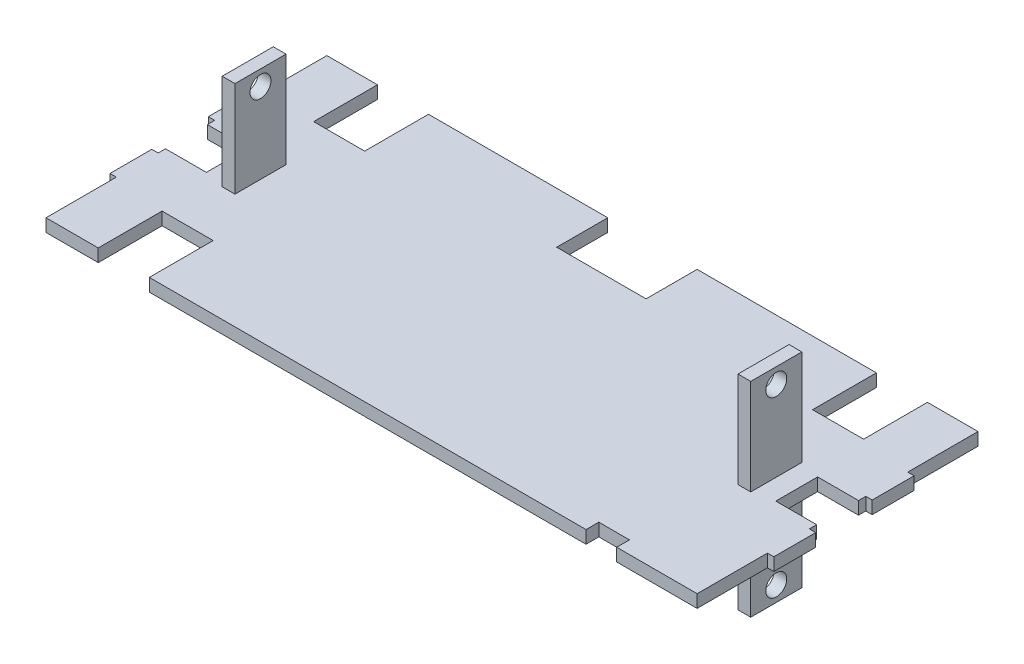
SolidWorks part; units mm, degrees
ref_plane "Front Plane" through (0, 0, 0) normal (0, 0, 1) x (1, 0, 0)
ref_plane "Top Plane" through (0, 0, 0) normal (0, 1, 0) x (1, 0, 0)
ref_plane "Right Plane" through (0, 0, 0) normal (1, 0, 0) x (0, 0, -1)
sketch "Sketch1" plane through (0, 0, 0) normal (0, 1, 0) x (1, 0, 0)
  line L1 (161.925, -69.85) -> (121.92, -69.85)
  line L2 (161.925, -69.85) -> (161.925, -34.8747)
  line L3 (161.925, 69.85) -> (136.779, 69.85)
  line L4 (-161.925, -69.85) -> (-161.925, -34.8747)
  line L5 (161.925, -69.85) -> (-161.925, 69.85) construction
  line L6 (161.925, 69.85) -> (-161.925, -69.85) construction
  line L7 (161.925, 10.414) -> (141.605, 10.414)
  line L9 (161.925, -10.414) -> (141.605, -10.414)
  line L10 (141.605, 10.414) -> (141.605, -10.414)
  line L11 (-136.779, 69.85) -> (-161.925, 69.85)
  line L13 (-161.925, -10.414) -> (-141.605, -10.414)
  line L14 (-141.605, 10.414) -> (-141.605, -10.414)
  line L15 (-161.925, 10.414) -> (-141.605, 10.414)
  line L17 (-141.605, 0) -> (141.605, 0) construction
  line L18 (-161.925, 14.0467) -> (-165.1, 14.0467)
  line L20 (-161.925, 34.8747) -> (-165.1, 34.8747)
  line L21 (-165.1, 14.0467) -> (-165.1, 34.8747)
  line L22 (-161.925, -34.8747) -> (-165.1, -34.8747)
  line L23 (-165.1, -14.0467) -> (-165.1, -34.8747)
  line L24 (-161.925, -14.0467) -> (-165.1, -14.0467)
  line L27 (161.925, -14.0467) -> (165.1, -14.0467)
  line L28 (165.1, -14.0467) -> (165.1, -34.8747)
  line L29 (161.925, -34.8747) -> (165.1, -34.8747)
  line L30 (161.925, 34.8747) -> (165.1, 34.8747)
  line L31 (165.1, 14.0467) -> (165.1, 34.8747)
  line L32 (161.925, 14.0467) -> (165.1, 14.0467)
  line L34 (-161.925, 34.8747) -> (-161.925, 69.85)
  line L35 (-161.925, -14.0467) -> (-161.925, -10.414)
  line L36 (161.925, 34.8747) -> (161.925, 69.85)
  line L37 (161.925, -14.0467) -> (161.925, -10.414)
  line L38 (-161.925, 10.414) -> (-161.925, 14.0467)
  line L39 (161.925, 10.414) -> (161.925, 14.0467)
  line L40 (-136.779, 69.85) -> (-136.779, 38.1)
  line L41 (-136.779, 38.1) -> (-111.379, 38.1)
  line L42 (-111.379, 69.85) -> (-111.379, 38.1)
  line L44 (111.379, 69.85) -> (111.379, 38.1)
  line L45 (111.379, 38.1) -> (136.779, 38.1)
  line L46 (136.779, 69.85) -> (136.779, 38.1)
  line L47 (111.379, 69.85) -> (22.2286, 69.85)
  line L48 (106.68, -69.85) -> (-106.68, -69.85)
  line L50 (106.68, -69.85) -> (106.68, -63.5)
  line L51 (106.68, -63.5) -> (121.92, -63.5)
  line L52 (121.92, -69.85) -> (121.92, -63.5)
  line L56 (-135.9408, -69.85) -> (-161.925, -69.85)
  line L57 (-106.68, -69.85) -> (-110.5408, -69.85)
  line L59 (-135.9408, -69.85) -> (-135.9408, -38.1)
  line L60 (-135.9408, -38.1) -> (-110.5408, -38.1)
  line L61 (-110.5408, -69.85) -> (-110.5408, -38.1)
  line L62 (-22.2286, 69.85) -> (-111.379, 69.85)
  line L64 (22.2286, 69.85) -> (22.2286, 44.45)
  line L65 (22.2286, 44.45) -> (-22.2286, 44.45)
  line L66 (-22.2286, 69.85) -> (-22.2286, 44.45)
  line L69 (0, 44.45) -> (0, -70.0261) construction
  point P0 (0, 0)
  point P6 (141.605, 0)
  point P11 (141.605, 0)
  point P47 (121.92, -66.675)
  point P48 (124.079, 38.1)
  point P49 (-124.079, 38.1)
  point P50 (0, 63.5)
  point P52 (-123.2408, -38.1)
  point P62 (0, 44.45)
  point P63 (0, 0)
  dimension "D1" = 323.85
  dimension "D2" = 139.7
  dimension "D3" = 20.828
  dimension "D5" = 3.175
  dimension "D6" = 20.828
  dimension "D4" = 20.32
  dimension "D7" = 31.75
  dimension "D8" = 25.4
  dimension "D9" = 25.4
  dimension "D10" = 31.75
  dimension "D13" = 15.24
  dimension "D14" = 6.35
  dimension "D15" = 40.005
  dimension "D16" = 25.4
  dimension "D17" = 31.75
  dimension "D18" = 41.8592
  dimension "D11" = 41.021
  dimension "D12" = 41.021
  dimension "D19" = 25.4
  dimension "D20" = 44.4572
  dimension "D21" = 3.6327
  dimension "D22" = 3.6327
  dimension "D25" = 20.828
  dimension "D26" = 20.828
  dimension "D28" = 20.828
  dimension "D29" = 3.6327
  dimension "D30" = 20.828
  dimension "D31" = 3.6327
  dimension "D32" = 20.828
  dimension "D23" = 20.32
extrude "Boss-Extrude1" add sketch "Sketch1" along normal mid plane 6.35
sketch "Sketch2" plane through (0, 0, 0) normal (0, 1, 0) x (1, 0, 0)
  line L0 (-141.605, 10.414) -> (-141.605, -10.414) construction
  line L1 (125.095, -12.7) -> (131.445, -12.7)
  line L2 (125.095, -12.7) -> (125.095, 12.7)
  line L3 (125.095, 12.7) -> (131.445, 12.7)
  line L4 (131.445, -12.7) -> (131.445, 12.7)
  line L5 (125.095, -12.7) -> (131.445, 12.7) construction
  line L6 (125.095, 12.7) -> (131.445, -12.7) construction
  line L9 (-125.095, -12.7) -> (-125.095, 12.7)
  line L10 (-125.095, 12.7) -> (-131.445, 12.7)
  line L11 (-131.445, -12.7) -> (-131.445, 12.7)
  line L12 (-125.095, -12.7) -> (-131.445, -12.7)
  line L13 (141.605, -10.414) -> (141.605, 10.414) construction
  point P0 (128.27, 0)
  point P10 (141.605, 0)
  dimension "D1" = 10.16
  dimension "D2" = 10.16
  dimension "D3" = 25.4
  dimension "D4" = 25.4
  dimension "D5" = 6.35
  dimension "D6" = 6.35
  dimension "D7" = 6.35
extrude "Boss-Extrude2" add sketch "Sketch2" along normal mid plane 101.6
sketch "Sketch3" plane through (-131.445, 0, 0) normal (-1, 0, 0) x (0, 0, 1)
  line L0 (-12.7, 50.8) -> (12.7, 50.8) construction
  line L1 (-12.7, -50.8) -> (12.7, -50.8) construction
  circle A0 centre (0, 43.18) radius 5.207
  circle A1 centre (0, -43.18) radius 5.207
  point P4 (0, 50.8)
  dimension "D1" = 10.414
  dimension "D2" = 10.414
  dimension "D3" = 7.62
  dimension "D4" = 7.62
  dimension "D5" = 86.36
extrude "Cut-Extrude1" cut sketch "Sketch3" against normal through all both and the other way through all
equation "\"length\"= 12.75"
equation "\"width\"=5.5"
equation "\"height\"= 0.25"
equation "\"D1@Sketch1\"=\"length\""
equation "\"D2@Sketch1\"=\"width\""
equation "\"eyebolt width\"= 0.82"
equation "\"eyebolt length\"= 0.8"
equation "\"D3@Sketch1\"=\"eyebolt width\""
equation "\"D4@Sketch1\"=\"eyebolt length\""
equation "\"lead screw holder height\"= 2.76"
equation "\"lead screw diameter\"=0.41"
equation "\"D1@Sketch3\"=\"lead screw diameter\""
equation "\"distance from holders to board\"=0.4"
equation "\"D2@Sketch3\"=\"lead screw diameter\""
equation "\"lead_screw_dist\"=3.4"
equation "\"D5@Sketch3\"=\"lead_screw_dist\""
